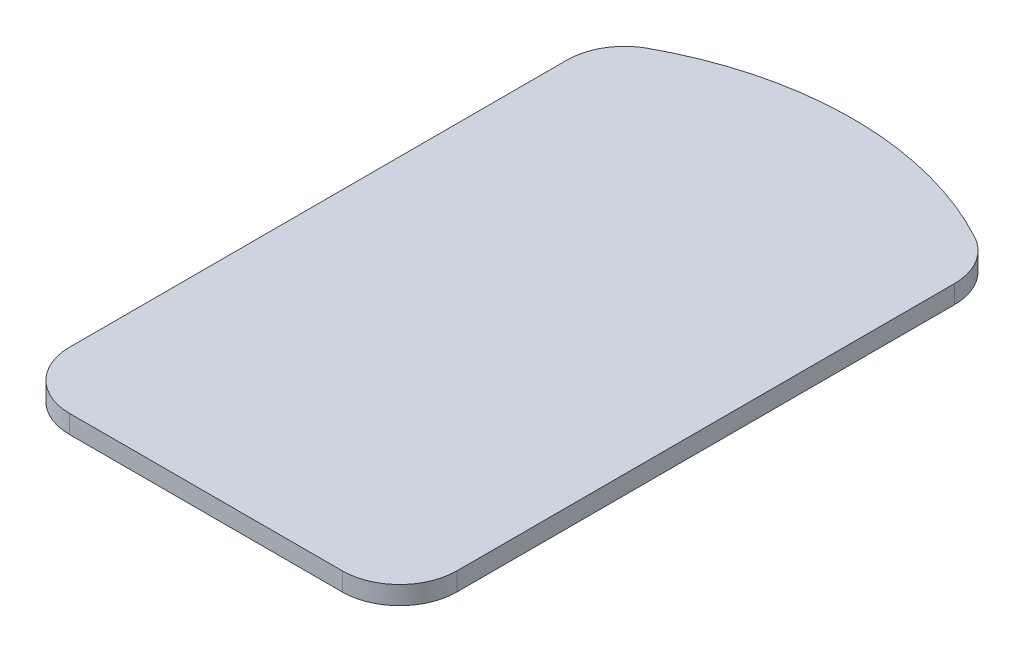
SolidWorks part; units mm, degrees
ref_plane "Front Plane" through (0, 0, 0) normal (0, 0, 1) x (1, 0, 0)
ref_plane "Top Plane" through (0, 0, 0) normal (0, 1, 0) x (1, 0, 0)
ref_plane "Right Plane" through (0, 0, 0) normal (1, 0, 0) x (0, 0, -1)
sketch "Sketch2" plane through (0, 0, 0) normal (0, 1, 0) x (1, 0, 0)
  line L0 (-83.3059, -49.0671) -> (-83.3059, 2.107)
  line L2 (-117.0879, -49.0671) -> (-117.0879, 2.107)
  line L14 (-117.0879, -49.0671) -> (-83.3059, -49.0671)
  arc A2 (-117.0879, 2.107) -> (-83.3059, 2.107) centre (-100.1969, -22.5043) cw
  point P0 (-100.1969, -49.0671)
extrude "Boss-Extrude1" add sketch "Sketch2" along normal blind 1.6
fillet "Fillet1" radius 5 4 edges at (-117.0879, 0.8, 49.0671) (-83.3059, 0.8, 49.0671) (-117.0879, 0.8, -2.107) (-83.3059, 0.8, -2.107)
